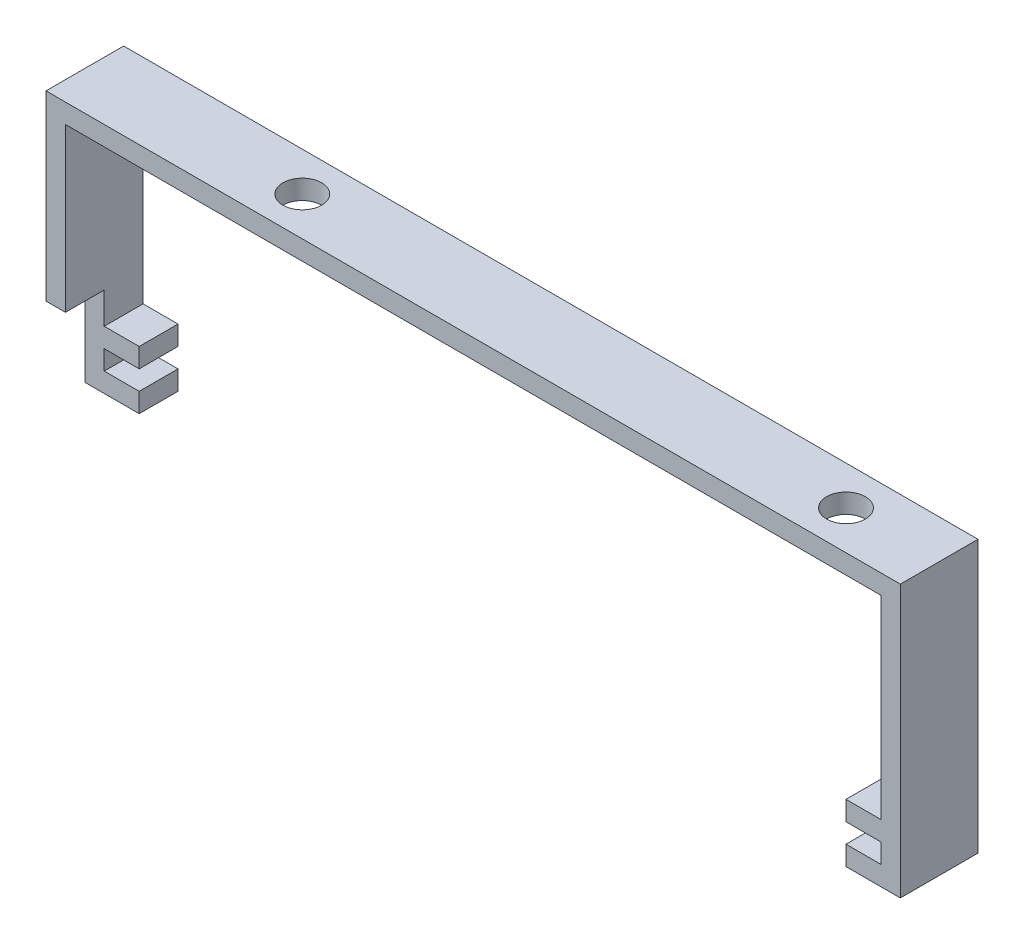
SolidWorks part; units mm, degrees
ref_plane "Front Plane" through (0, 0, 0) normal (0, 0, 1) x (1, 0, 0)
ref_plane "Top Plane" through (0, 0, 0) normal (0, 1, 0) x (1, 0, 0)
ref_plane "Right Plane" through (0, 0, 0) normal (1, 0, 0) x (0, 0, -1)
sketch "Sketch1" plane through (0, 0, 0) normal (0, 0, 1) x (1, 0, 0)
  line L0 (2.5, -30) -> (2.5, -32.5)
  line L1 (0, 0) -> (110, 0)
  line L2 (0, 0) -> (0, -2.5)
  line L3 (2.5, -2.5) -> (107.5, -2.5)
  line L4 (110, 0) -> (110, -2.5)
  line L6 (0, -2.5) -> (0, -32.5)
  line L8 (2.5, -2.5) -> (2.5, -27.5)
  line L10 (110, -2.5) -> (110, -32.5)
  line L12 (107.5, -2.5) -> (107.5, -27.5)
  line L13 (2.5, -32.5) -> (7, -32.5)
  line L14 (0, -32.5) -> (0, -35)
  line L15 (0, -35) -> (7, -35)
  line L16 (7, -32.5) -> (7, -35)
  line L17 (2.5, -30) -> (7, -30)
  line L19 (2.5, -27.5) -> (7, -27.5)
  line L20 (7, -30) -> (7, -27.5)
  line L21 (107.5, -30) -> (107.5, -32.5)
  line L22 (107.5, -32.5) -> (103, -32.5)
  line L23 (110, -32.5) -> (110, -35)
  line L24 (110, -35) -> (103, -35)
  line L25 (103, -32.5) -> (103, -35)
  line L26 (107.5, -27.5) -> (103, -27.5)
  line L28 (107.5, -30) -> (103, -30)
  line L29 (103, -27.5) -> (103, -30)
  dimension "D1" = 110
  dimension "D2" = 2.5
  dimension "D3" = 2.5
  dimension "D4" = 30
  dimension "D5" = 30
  dimension "D6" = 2.5
  dimension "D7" = 2.5
  dimension "D8" = 7
  dimension "D9" = 2.5
  dimension "D10" = 2.5
  dimension "D11" = 7
  dimension "D12" = 2.5
  dimension "D13" = 2.5
  dimension "D14" = 2.5
extrude "Boss-Extrude1" add sketch "Sketch1" along normal blind 10
sketch "Sketch2" plane through (0, 0, 10) normal (0, 0, 1) x (1, 0, 0)
  line L1 (0, -35) -> (7.883, -35)
  line L2 (0, -35) -> (0, -23.4499)
  line L3 (0, -23.4499) -> (7.883, -23.4499)
  line L4 (7.883, -35) -> (7.883, -23.4499)
extrude "Cut-Extrude1" cut sketch "Sketch2" against normal blind 5
sketch "Sketch3" plane through (0, 0, 0) normal (0, 1, 0) x (1, 0, 0)
  line L0 (110, -10) -> (110, 0) construction
  circle A0 centre (98, -5) radius 2.5
  circle A1 centre (28, -5) radius 2.5
  dimension "D1" = 5
  dimension "D2" = 12
  dimension "D3" = 5
  dimension "D4" = 70
extrude "Cut-Extrude2" cut sketch "Sketch3" against normal blind 3
